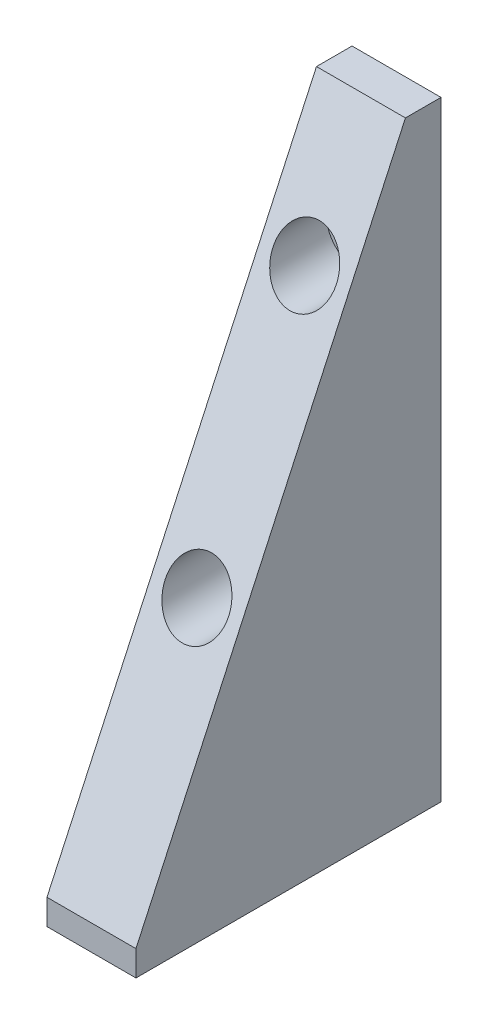
SolidWorks part; units mm, degrees
ref_plane "Front Plane" through (0, 0, 0) normal (0, 0, 1) x (1, 0, 0)
ref_plane "Top Plane" through (0, 0, 0) normal (0, 1, 0) x (1, 0, 0)
ref_plane "Right Plane" through (0, 0, 0) normal (1, 0, 0) x (0, 0, -1)
sketch "Sketch1" plane through (0, 0, 0) normal (1, 0, 0) x (0, 0, -1)
  line L0 (21.526, 126.619) -> (-45.784, -19.431)
  line L1 (-45.784, -25.781) -> (30.416, -25.781)
  line L2 (30.416, -25.781) -> (30.416, 126.619)
  line L3 (30.416, 88.4519) -> (3.9359, 88.4519) construction
  line L4 (21.526, 126.619) -> (30.416, 126.619)
  line L5 (-45.784, -19.431) -> (-45.784, -25.781)
  line L6 (30.416, 59.5647) -> (-9.3773, 59.5647) construction
  dimension "D1" = 76.2
  dimension "D2" = 152.4
  dimension "D3" = 8.89
  dimension "D4" = 6.35
extrude "Boss-Extrude2" add sketch "Sketch1" along normal blind 22.225
sketch "Sketch2" plane through (0, 0, 0) normal (-1, 0, 0) x (0, 0, 1)
  line L0 (-30.416, 96.139) -> (-11.366, 96.139) construction
  line L2 (-30.416, -25.781) -> (-30.416, 126.619) construction
  line L3 (-30.416, 37.719) -> (-10.096, 37.719) construction
  line L4 (-30.416, 126.619) -> (-21.526, 126.619) construction
  point P8 (-25.971, 126.619)
  dimension "D1" = 30.48
  dimension "D2" = 88.9
  dimension "D3" = 19.05
  dimension "D4" = 20.32
ref_plane "Plane1" through (0, 96.139, -11.366) normal (0, 0, 1) x (1, 0, 0)
ref_plane "Plane2" through (0, 37.719, -10.096) normal (0, 0, 1) x (1, 0, 0)
hole_wizard "CBORE for 3/8 Socket Head Cap Screw1" positions "Sketch3" profile "Sketch4" counterbore size "3/8" standard "ANSI Inch"
sketch "Sketch3" plane through (0, 96.139, -11.366) normal (0, 0, 1) x (1, 0, 0)
  line L0 (0, 30.48) -> (0, -115.57) construction
  line L1 (22.225, 30.48) -> (0, 30.48) construction
  point P0 (11.1125, 0)
  point P8 (11.1125, 30.48)
  dimension "D1" = 11.1125
  dimension "D2" = 30.48
sketch "Sketch4" plane through (11.1125, 96.139, -11.366) normal (1, 0, 0) x (0, -1, 0)
  line L0 (0, 0) -> (0, 19.05)
  line L1 (0, 19.05) -> (4.9022, 19.05)
  line L3 (4.9022, 19.05) -> (4.9022, 9.525)
  line L4 (4.9022, 9.525) -> (7.9375, 9.525)
  line L5 (7.9375, 9.525) -> (7.9375, 0)
  line L7 (7.9375, 0) -> (0, 0)
  line L11 (0, -6.35) -> (0, 107.95) construction
  dimension "Thru Hole Dia." = 9.8044
  dimension "Thru Hole Depth" = 19.05
  dimension "C'Bore Dia." = 15.875
  dimension "C'Bore Depth" = 9.525
hole_wizard "CBORE for 3/8 Socket Head Cap Screw2" positions "Sketch5" profile "Sketch6" counterbore size "3/8" standard "ANSI Inch"
sketch "Sketch5" plane through (0, 37.719, -10.096) normal (0, 0, 1) x (1, 0, 0)
  line L0 (0, -63.5) -> (0, 88.9) construction
  line L3 (22.225, 88.9) -> (0, 88.9) construction
  point P0 (11.1125, 0)
  point P13 (11.1125, 88.9)
  dimension "D1" = 11.1125
  dimension "D2" = 88.9
sketch "Sketch6" plane through (11.1125, 37.719, -10.096) normal (1, 0, 0) x (0, -1, 0)
  line L0 (0, 0) -> (0, 20.32)
  line L1 (0, 20.32) -> (4.9022, 20.32)
  line L3 (4.9022, 20.32) -> (4.9022, 9.525)
  line L4 (4.9022, 9.525) -> (7.9375, 9.525)
  line L5 (7.9375, 9.525) -> (7.9375, 0)
  line L7 (7.9375, 0) -> (0, 0)
  line L11 (0, -6.35) -> (0, 107.95) construction
  dimension "Thru Hole Dia." = 9.8044
  dimension "Thru Hole Depth" = 20.32
  dimension "C'Bore Dia." = 15.875
  dimension "C'Bore Depth" = 9.525
sketch "Sketch7" plane through (0, 96.139, -11.366) normal (0, 0, 1) x (1, 0, 0)
  circle A0 centre (11.1125, -58.42) radius 7.9375 construction
  circle A1 centre (11.1125, 0) radius 7.9375 construction
  circle A2 centre (11.1125, -58.42) radius 7.9375
  circle A3 centre (11.1125, 0) radius 7.9375
extrude "Cut-Extrude2" cut sketch "Sketch7" along normal up to next
hole_wizard "3/8-16 Tapped Hole1" positions "3DSketch4" profile "Sketch9" tap size "3/8-16" standard "ANSI Inch"
sketch3d "3DSketch4"
  line L0 (22.225, -25.781, -30.416) -> (0, -25.781, -30.416) construction
  line L2 (0, -25.781, 45.784) -> (0, -25.781, -30.416) construction
  point P0 (11.1125, -25.781, -15.176)
  point P2 (11.1125, -25.781, 25.464)
  dimension "D1" = 15.24
  dimension "D2" = 40.64
  dimension "D3" = 11.1125
  dimension "D4" = 11.1125
sketch "Sketch9" plane through (11.1125, -25.781, -15.176) normal (1, 0, 0) x (0, 0, -1)
  line L0 (0, 0) -> (0, 27.7847)
  line L1 (0, 27.7847) -> (3.9687, 25.4)
  line L2 (3.9687, 25.4) -> (3.9687, 0)
  line L5 (3.9687, 0) -> (0, 0)
  line L10 (0, 27.7847) -> (-3.9688, 25.4) construction
  line L11 (0, -6.35) -> (0, 107.95) construction
  dimension "Tap Drill Dia." = 7.9375
  dimension "Tap Drill Depth" = 25.4
  dimension "Drill Angle" = 118
cosmetic thread "Hole Thread1" parameters "D1"=20.32, "D2"=9.525
cosmetic thread "Hole Thread2" parameters "D1"=20.32, "D2"=9.525
